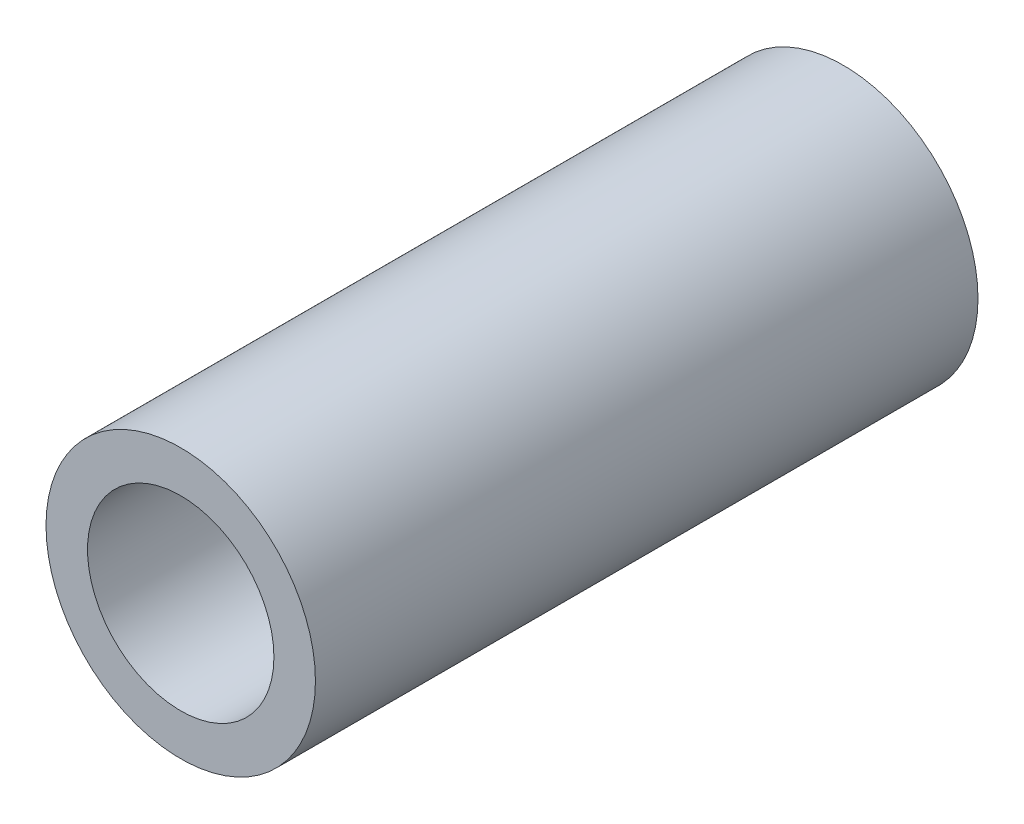
SolidWorks part; units mm, degrees
material "PVC Rigid"
ref_plane "Front Plane" through (0, 0, 0) normal (0, 0, 1) x (1, 0, 0)
ref_plane "Top Plane" through (0, 0, 0) normal (0, 1, 0) x (1, 0, 0)
ref_plane "Right Plane" through (0, 0, 0) normal (1, 0, 0) x (0, 0, -1)
sketch "Sketch1" plane through (0, 0, 0) normal (0, 0, 1) x (1, 0, 0)
  circle A0 centre (0, 0) radius 7.747
  circle A1 centre (0, 0) radius 5.3594
  dimension "D1" = 15.494
  dimension "D2" = 10.7188
extrude "Boss-Extrude1" add sketch "Sketch1" along normal blind 38.1
